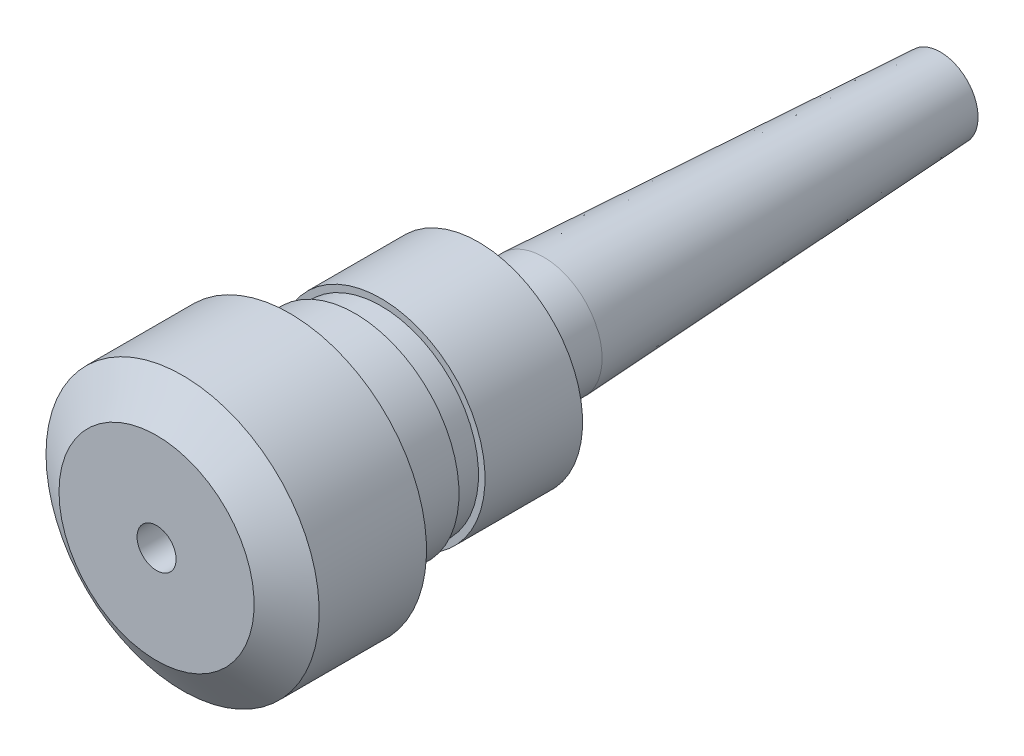
SolidWorks part; units mm, degrees
ref_plane "Front Plane" through (0, 0, 0) normal (0, 0, 1) x (1, 0, 0)
ref_plane "Top Plane" through (0, 0, 0) normal (0, 1, 0) x (1, 0, 0)
ref_plane "Right Plane" through (0, 0, 0) normal (1, 0, 0) x (0, 0, -1)
sketch "Sketch1" plane through (0, 0, 0) normal (0, 1, 0) x (1, 0, 0)
  line L0 (0, 75.909) -> (0, -75.6707) construction
  line L1 (3, 0) -> (15, 0)
  line L2 (15, 0) -> (21, 4)
  line L3 (21, 4) -> (21, 20.5)
  line L4 (21, 20.5) -> (16, 20.5)
  line L5 (16, 20.5) -> (16, 30.5)
  line L6 (16, 30.5) -> (15, 30.5)
  line L7 (15, 30.5) -> (15, 34.5)
  line L8 (15, 34.5) -> (16, 34.5)
  line L9 (16, 34.5) -> (16, 49.5)
  line L10 (16, 49.5) -> (0, 49.5)
  line L11 (0, 49.5) -> (0, 30)
  line L12 (3, 0) -> (3, 30)
  line L13 (3, 30) -> (0, 30)
  line L14 (-7.3332, 0) -> (20.2921, 0) construction
  dimension "D2" = 21
  dimension "D3" = 16
  dimension "D4" = 15
  dimension "D5" = 16
  dimension "D6" = 15
  dimension "D7" = 4
  dimension "D8" = 10
  dimension "D9" = 4
  dimension "D10" = 16.5
  dimension "D11" = 15
  dimension "D12" = 6
  dimension "D13" = 30
revolve "Revolve1" add sketch "Sketch1" angle 360 about L0
sketch "Sketch2" plane through (0, 0, -49.5) normal (0, 0, -1) x (-1, 0, 0)
  circle A0 centre (0, 0) radius 9
  dimension "D1" = 18
extrude "Boss-Extrude1" add sketch "Sketch2" along normal blind 10
sketch "Sketch3" plane through (0, 0, -59.5) normal (0, 0, -1) x (-1, 0, 0)
  circle A0 centre (0, 0) radius 9 construction
  circle A1 centre (0, 0) radius 9
extrude "Boss-Extrude2" add sketch "Sketch3" along normal blind 61 draft 3
sketch "Sketch4" plane through (0, 0, -120.5) normal (0, 0, -1) x (-1, 0, 0)
  circle A0 centre (0, 0) radius 4
  dimension "D1" = 8
extrude "Cut-Extrude1" cut sketch "Sketch4" against normal blind 61
